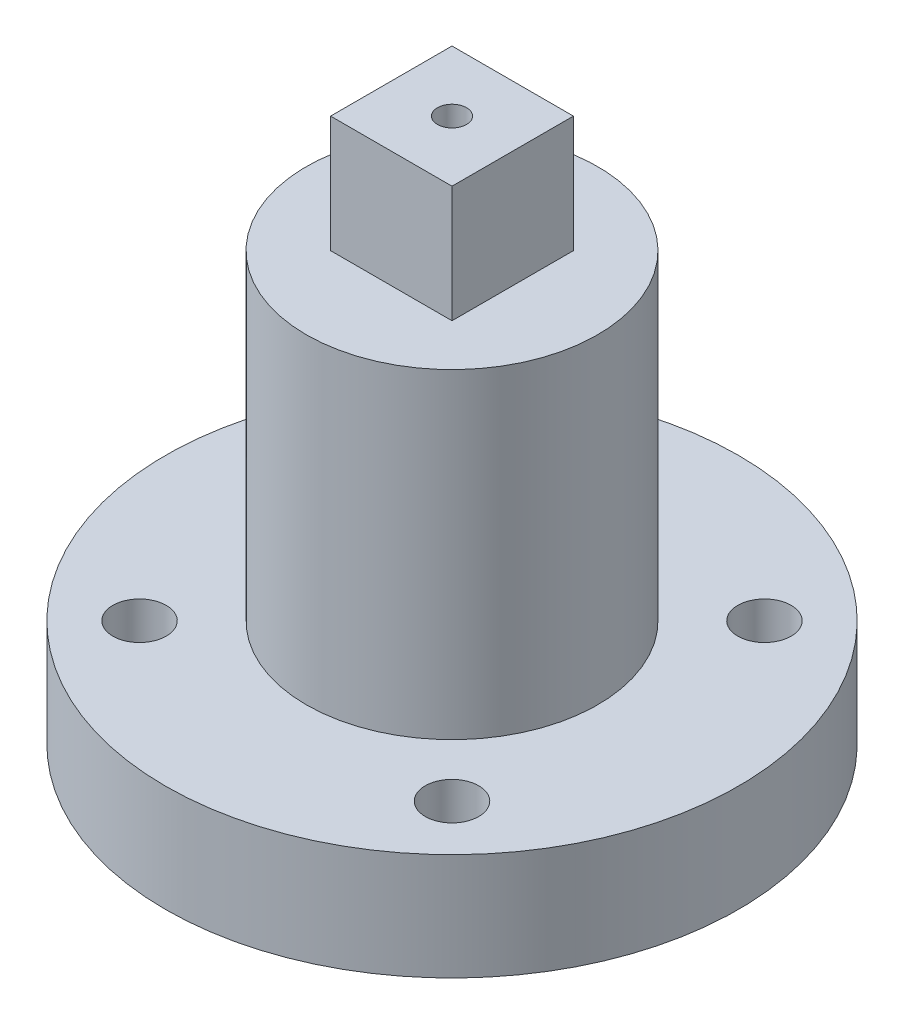
SolidWorks part; units mm, degrees
ref_plane "前视基准面" through (0, 0, 0) normal (0, 0, 1) x (1, 0, 0)
ref_plane "上视基准面" through (0, 0, 0) normal (0, 1, 0) x (1, 0, 0)
ref_plane "右视基准面" through (0, 0, 0) normal (1, 0, 0) x (0, 0, -1)
sketch "草图1" plane through (0, 0, 0) normal (0, 1, 0) x (1, 0, 0)
  circle A0 centre (0, 0) radius 29.5
extrude "凸台-拉伸1" add sketch "草图1" along normal blind 11
sketch "草图2" plane through (0, 11, 0) normal (0, 1, 0) x (1, 0, 0)
  circle A0 centre (0, 0) radius 15
extrude "凸台-拉伸2" add sketch "草图2" along normal blind 33
sketch "草图3" plane through (0, 44, 0) normal (0, 1, 0) x (1, 0, 0)
  line L1 (6.25, 6.25) -> (-6.25, 6.25)
  line L2 (6.25, 6.25) -> (6.25, -6.25)
  line L3 (6.25, -6.25) -> (-6.25, -6.25)
  line L4 (-6.25, 6.25) -> (-6.25, -6.25)
  line L5 (6.25, 6.25) -> (-6.25, -6.25) construction
  line L6 (6.25, -6.25) -> (-6.25, 6.25) construction
  point P0 (0, 0)
extrude "凸台-拉伸3" add sketch "草图3" along normal blind 12
sketch "草图4" plane through (0, 11, 0) normal (0, 1, 0) x (1, 0, 0)
  line L0 (-6.25, -6.25) -> (16.0867, 16.0867) construction
  line L4 (-6.25, 6.25) -> (-6.25, -6.25)
  line L5 (-6.25, -6.25) -> (6.25, -6.25)
  line L6 (6.25, -6.25) -> (6.25, 6.25)
  line L7 (6.25, 6.25) -> (-6.25, 6.25)
  line L8 (-6.25, 6.25) -> (-6.25, -6.25) construction
  line L9 (-6.25, -6.25) -> (6.25, -6.25) construction
  line L10 (6.25, -6.25) -> (6.25, 6.25) construction
  line L11 (6.25, 6.25) -> (-6.25, 6.25) construction
  circle A0 centre (0, 0) radius 22.75 construction
  circle A2 centre (16.0867, 16.0867) radius 2.75
  dimension "D1" = 0
extrude "切除-拉伸1" cut sketch "草图4" against normal blind 12
pattern_circular "阵列(圆周)1" count 4 over 360 about axis through (0, 0, 0) along (0, 1, 0) of "切除-拉伸1"
sketch "草图5" plane through (0, 56, 0) normal (0, 1, 0) x (1, 0, 0)
  circle A0 centre (0, 0) radius 1.5
extrude "切除-拉伸2" cut sketch "草图5" against normal blind 10
